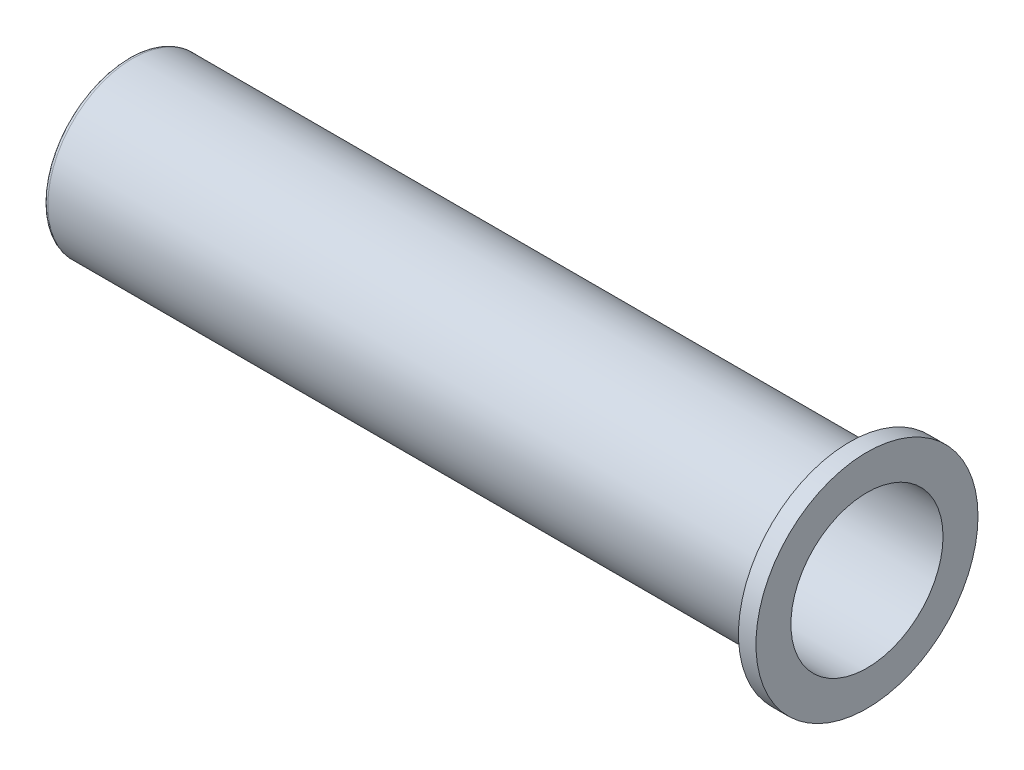
SolidWorks part; units mm, degrees
material "ABS PC"
ref_plane "Front Plane" through (0, 0, 0) normal (0, 0, 1) x (1, 0, 0)
ref_plane "Top Plane" through (0, 0, 0) normal (0, 1, 0) x (1, 0, 0)
ref_plane "Right Plane" through (0, 0, 0) normal (1, 0, 0) x (0, 0, -1)
sketch "Sketch1" plane through (0, 0, 0) normal (0, 1, 0) x (1, 0, 0)
  line L0 (0, 0) -> (-35, 0) construction
  line L2 (-35, 4.35) -> (6.75, 4.35)
  line L3 (-35, 4.35) -> (-35, 4.85)
  line L4 (-35, 4.85) -> (5.75, 4.85)
  line L5 (5.75, 4.85) -> (5.75, 6.35)
  line L6 (5.75, 6.35) -> (6.75, 6.35)
  line L7 (6.75, 6.35) -> (6.75, 4.35)
  dimension "D1" = 35
  dimension "D2" = 4.35
  dimension "D3" = 0.5
  dimension "D4" = 2
  dimension "D5" = 40.75
  dimension "D6" = 41.75
revolve "Revolve1" add sketch "Sketch1" angle 360 about L0
sketch "Sketch2" plane through (-35, 0, 0) normal (-1, 0, 0) x (0, 0, 1)
  circle A0 centre (0, 0) radius 4.85
  circle A1 centre (0, 0) radius 2.75
  circle A2 centre (0, 0) radius 4.85 construction
  dimension "D1" = 5.5
extrude "Boss-Extrude1" add sketch "Sketch2" along normal blind 0.5
fillet "Fillet1" radius 0.25 2 edges at (-35, 0, -4.35) (-35.5, 0, 4.85)
